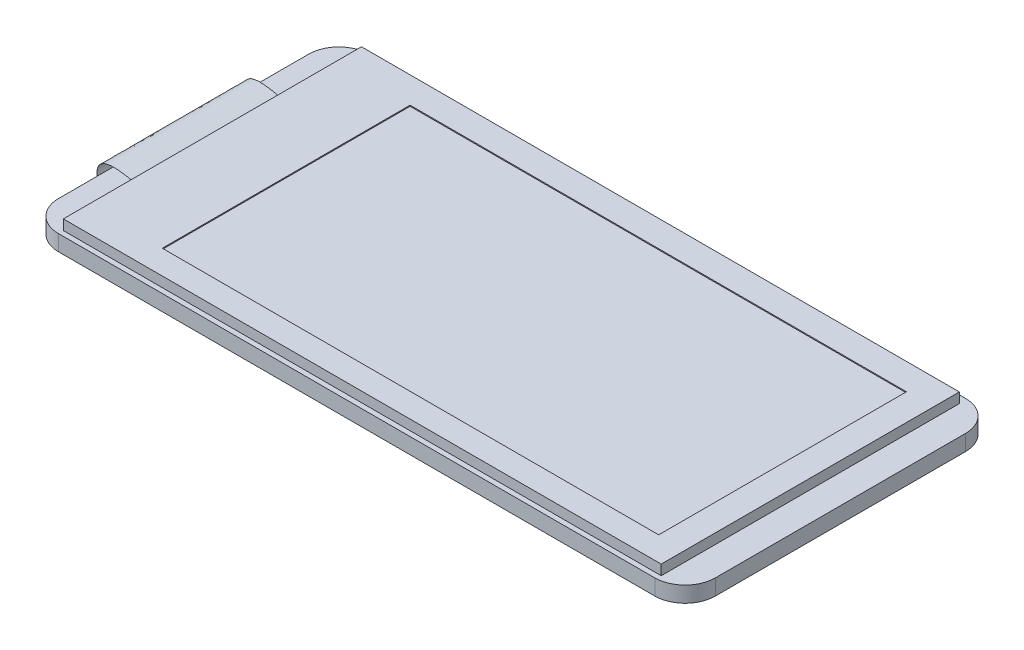
SolidWorks part; units mm, degrees
ref_plane "前视基准面" through (0, 0, 0) normal (0, 0, 1) x (1, 0, 0)
ref_plane "上视基准面" through (0, 0, 0) normal (0, 1, 0) x (1, 0, 0)
ref_plane "右视基准面" through (0, 0, 0) normal (1, 0, 0) x (0, 0, -1)
sketch "草图1" plane through (0, 0, 0) normal (0, 1, 0) x (1, 0, 0)
  line L1 (-29.5, 15.375) -> (29.5, 15.375)
  line L2 (-32.5, 12.375) -> (-32.5, -12.375)
  line L3 (-29.5, -15.375) -> (29.5, -15.375)
  line L4 (32.5, 12.375) -> (32.5, -12.375)
  line L5 (-32.5, 15.375) -> (32.5, -15.375) construction
  line L6 (-32.5, -15.375) -> (32.5, 15.375) construction
  arc A0 (-32.5, -12.375) -> (-29.5, -15.375) centre (-29.5, -12.375) ccw
  arc A1 (29.5, -15.375) -> (32.5, -12.375) centre (29.5, -12.375) ccw
  arc A2 (29.5, 15.375) -> (32.5, 12.375) centre (29.5, 12.375) cw
  arc A3 (-29.5, 15.375) -> (-32.5, 12.375) centre (-29.5, 12.375) ccw
  point P0 (0, 0)
  dimension "D3" = 3
  dimension "D1" = 30.75
  dimension "D2" = 65
extrude "凸台-拉伸1" add sketch "草图1" along normal blind 1.56
sketch "草图3" plane through (0, 1.56, 0) normal (0, 1, 0) x (1, 0, 0)
  line L0 (-29.5, -15.375) -> (29.5, -15.375) construction
  line L1 (-29.52, 14.625) -> (29.64, 14.625)
  line L2 (-29.52, 14.625) -> (-29.52, -14.875)
  line L3 (-29.52, -14.875) -> (29.64, -14.875)
  line L4 (29.64, 14.625) -> (29.64, -14.875)
  line L5 (-32.5, 12.375) -> (-32.5, -12.375) construction
  line L7 (32.5, -12.375) -> (32.5, 12.375) construction
  dimension "D1" = 29.5
  dimension "D2" = 2.98
  dimension "D3" = 0.5
  dimension "D4" = 2.86
extrude "凸台-拉伸2" add sketch "草图3" along normal blind 1
sketch "草图8" plane through (0, 0, 0) normal (0, -1, 0) x (1, 0, 0)
  line L0 (29.5, -15.375) -> (-29.5, -15.375) construction
  line L1 (-25.7, -8.735) -> (25.3, -8.735)
  line L2 (-25.7, -8.735) -> (-25.7, -13.735)
  line L3 (-25.7, -13.735) -> (25.3, -13.735)
  line L4 (25.3, -8.735) -> (25.3, -13.735)
  line L5 (32.5, 12.375) -> (32.5, -12.375) construction
  dimension "D1" = 5
  dimension "D2" = 51
  dimension "D3" = 1.64
  dimension "D4" = 7.2
extrude "凸台-拉伸6" add sketch "草图8" along normal blind 3.68
sketch "草图9" plane through (0, 2.56, 0) normal (0, 1, 0) x (1, 0, 0)
  line L0 (-32.5, 12.375) -> (-32.5, -12.375) construction
  line L1 (-22.11, 12.025) -> (27.01, 12.025)
  line L2 (-22.11, 12.025) -> (-22.11, -12.495)
  line L3 (-22.11, -12.495) -> (27.01, -12.495)
  line L4 (27.01, 12.025) -> (27.01, -12.495)
  line L5 (32.5, -12.375) -> (32.5, 12.375) construction
  line L6 (-29.5, -15.375) -> (29.5, -15.375) construction
  line L7 (29.5, 15.375) -> (-29.5, 15.375) construction
  dimension "D1" = 10.39
  dimension "D2" = 5.49
  dimension "D3" = 2.88
  dimension "D4" = 3.35
extrude "切除-拉伸1" cut sketch "草图9" against normal blind 0.1
sketch3d "3D草图1"
  line L0 (-29.52, 1.56, -7.125) -> (-29.52, 1.56, 7.375)
  line L1 (-29.52, 1.56, -14.625) -> (-29.52, 1.56, 14.875) construction
  point P4 (-29.52, 1.56, -4.2162)
  point P6 (-29.52, 1.56, 3.0199)
  dimension "D1" = 7.5
  dimension "D2" = 7.5
sketch3d "3D草图5"
  line L0 (-29.5, 0, -7.375) -> (-29.5, 0, 7.375)
  line L1 (-29.5, 0, 15.375) -> (29.5, 0, 15.375) construction
  line L2 (29.5, 0, -15.375) -> (-29.5, 0, -15.375) construction
  dimension "D1" = 8
  dimension "D2" = 8
  dimension "D3" = 3
sketch3d "3D草图6"
  spline S0 degree 3 poles (-29.52, 1.56, -7.125) (-33.3668, 2.5745, -7.2105) (-34.1351, 0.0224, -7.0869) (-32.5097, -0.8636, -7.1266) (-29.5, 0, -7.375) knots 0 0 0 0 0.435437 1 1 1 1
  point P2 (0, 0, 0)
  point P4 (-33.5962, 1.0239, -7.1451)
surface "曲面-放样1"
